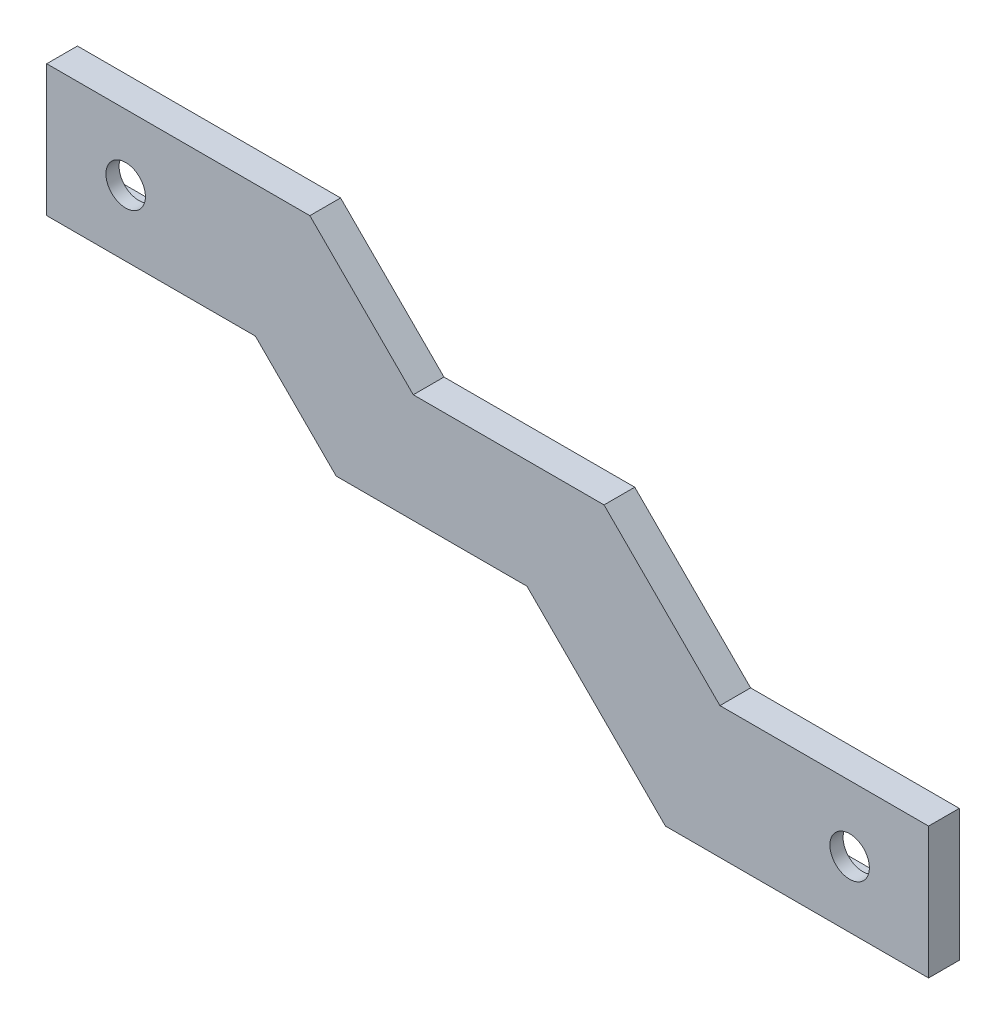
SolidWorks part; units mm, degrees
ref_plane "Спереди" through (0, 0, 0) normal (0, 0, 1) x (1, 0, 0)
ref_plane "Сверху" through (0, 0, 0) normal (0, 1, 0) x (1, 0, 0)
ref_plane "Справа" through (0, 0, 0) normal (1, 0, 0) x (0, 0, -1)
sketch "Эскиз1" plane through (0, 0, 0) normal (0, 0, 1) x (1, 0, 0)
  line L1 (112.7696, -7.5) -> (12.2304, -7.5)
  line L2 (112.7696, -7.5) -> (112.7696, 32.5)
  line L3 (112.7696, 32.5) -> (12.2304, 32.5)
  line L4 (12.2304, -7.5) -> (12.2304, 32.5)
  line L9 (32.7304, 21.5) -> (15.7304, 21.5)
  line L10 (32.7304, 21.5) -> (32.7304, 28.5)
  line L11 (32.7304, 28.5) -> (15.7304, 28.5)
  line L12 (15.7304, 21.5) -> (15.7304, 28.5)
  line L14 (16.2304, 22) -> (32.2304, 22) construction
  line L17 (50.7696, -3.5) -> (110.7696, -3.5) construction
  line L20 (110.7696, 3.5) -> (50.7696, 3.5) construction
  line L21 (109.2696, -3.5) -> (92.2696, -3.5)
  line L22 (109.2696, -3.5) -> (109.2696, 3.5)
  line L23 (109.2696, 3.5) -> (92.2696, 3.5)
  line L24 (92.2696, -3.5) -> (92.2696, 3.5)
  line L25 (108.7696, -3) -> (108.7696, 3) construction
  line L26 (92.7696, 3) -> (92.7696, -3) construction
  dimension "D1" = 0.5
  dimension "D2" = 17
  dimension "D3" = 7
  dimension "D4" = 0.5
  dimension "D5" = 0.5
extrude "Бобышка-Вытянуть1" add sketch "Эскиз1" along normal blind 2
sketch "Эскиз2" plane through (0, 0, 2) normal (0, 0, 1) x (1, 0, 0)
  line L1 (12.2304, 32.5) -> (112.7696, 32.5)
  line L2 (12.2304, 32.5) -> (12.2304, -7.5)
  line L3 (12.2304, -7.5) -> (112.7696, -7.5)
  line L4 (112.7696, 32.5) -> (112.7696, -7.5)
  circle A0 centre (21.2304, 25) radius 2.25
  circle A1 centre (103.7696, 0) radius 2.25
extrude "Бобышка-Вытянуть2" add sketch "Эскиз2" along normal blind 1.5
sketch "Эскиз3" plane through (0, 0, 3.5) normal (0, 0, 1) x (1, 0, 0)
  line L0 (12.2304, 32.5) -> (42.2304, 32.5)
  line L1 (112.7696, 32.5) -> (12.2304, 32.5) construction
  line L2 (42.2304, 32.5) -> (54.0204, 20.71)
  line L3 (54.0204, 20.71) -> (75.7696, 20.71)
  line L4 (75.7696, 20.71) -> (88.9796, 7.5)
  line L5 (88.9796, 7.5) -> (112.7696, 7.5)
  line L6 (112.7696, -7.5) -> (112.7696, 32.5) construction
  line L7 (112.7696, 7.5) -> (112.7696, -7.5)
  line L8 (112.7696, -7.5) -> (82.7696, -7.5)
  line L9 (12.2304, -7.5) -> (112.7696, -7.5) construction
  line L10 (82.7696, -7.5) -> (66.9828, 8.2868)
  line L11 (66.9828, 8.2868) -> (45.2304, 8.2868)
  line L12 (45.2304, 8.2868) -> (36.0172, 17.5)
  line L13 (36.0172, 17.5) -> (12.2304, 17.5)
  line L14 (12.2304, 32.5) -> (12.2304, -7.5) construction
  line L15 (12.2304, 17.5) -> (12.2304, 32.5)
  line L17 (-11.173, 55.2443) -> (173.6359, 55.2443)
  line L18 (-11.173, 55.2443) -> (-11.173, -39.5809)
  line L19 (-11.173, -39.5809) -> (173.6359, -39.5809)
  line L20 (173.6359, 55.2443) -> (173.6359, -39.5809)
  circle A0 centre (103.7696, 0) radius 1.25 construction
  circle A1 centre (21.2304, 25) radius 1.25 construction
  dimension "D4" = 7.5
  dimension "D1" = 45
  dimension "D2" = 45
  dimension "D3" = 7.5
  dimension "D5" = 7.5
  dimension "D6" = 45
  dimension "D7" = 15
  dimension "D8" = 30
  dimension "D9" = 30
  dimension "D10" = 23.7868
  dimension "D11" = 23.79
  dimension "D12" = 14.9977
  dimension "D13" = 33
  dimension "D14" = 37
extrude "Вырез-Вытянуть1" cut sketch "Эскиз3" against normal blind 31.5
sketch "Эскиз4" plane through (0, 0, 3.5) normal (0, 0, 1) x (1, 0, 0)
  line L1 (42.2304, 32.5) -> (12.2304, 32.5) construction
  line L3 (12.2304, 32.5) -> (12.2304, 17.5) construction
  circle A0 centre (32.2304, 28.5) radius 3.5
  point P5 (21.2304, 25)
  dimension "D1" = 7
  dimension "D3" = 20
  dimension "D2" = 4
extrude "Бобышка-Вытянуть3" [suppressed] add sketch "Эскиз4" along normal blind 10
